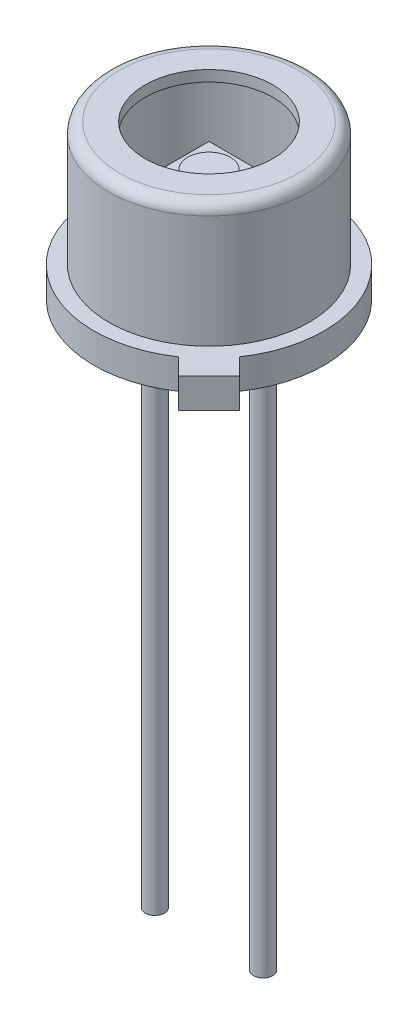
SolidWorks part; units mm, degrees
ref_plane "Front Plane" through (0, 0, 0) normal (0, 0, 1) x (1, 0, 0)
ref_plane "Top Plane" through (0, 0, 0) normal (0, 1, 0) x (1, 0, 0)
ref_plane "Right Plane" through (0, 0, 0) normal (1, 0, 0) x (0, 0, -1)
sketch "Sketch1" plane through (0, 0, 0) normal (0, 0, 1) x (1, 0, 0)
  line L0 (0, 0) -> (0, 37.7864) construction
  line L2 (2.7, 0) -> (2.7, 0.7)
  line L3 (2.7, 0.7) -> (2.35, 0.7)
  line L6 (2.35, 0.7) -> (2.35, 3.346)
  line L7 (2.096, 3.6) -> (1.5, 3.6)
  arc A0 (2.35, 3.346) -> (2.096, 3.6) centre (2.096, 3.346) ccw
  dimension "D7" = 0.254
  dimension "D1" = 0.7
  dimension "D2" = 4.7
  dimension "D4" = 5.4
  dimension "D6" = 3.6
  dimension "D8" = 3
revolve "Revolve-Thin2" add sketch "Sketch1" angle 360 about L0
sketch "Sketch2" plane through (0, 0, 0) normal (0, -1, 0) x (1, 0, 0)
  circle A1 centre (0, 0) radius 2.7
  circle A2 centre (0, 0) radius 2.7
  dimension "D1" = 0
extrude "Boss-Extrude1" add sketch "Sketch2" against normal up to surface (0.446 mm away) up to face at (0, 0.446, -2.096)
sketch "Sketch3" plane through (0, 0, 0) normal (0, -1, 0) x (1, 0, 0)
  line L0 (0.6, 0.6) -> (-0.6, -0.6) construction
  line L1 (-0.6, 0.6) -> (0.6, 0.6)
  line L2 (-0.6, 0.6) -> (-0.6, -0.6)
  line L3 (-0.6, -0.6) -> (0.6, -0.6)
  line L4 (0.6, 0.6) -> (0.6, -0.6)
  dimension "D1" = 1.2
extrude "Boss-Extrude2" add sketch "Sketch3" along normal blind 0.05 from offset 2.6 separate body offset against normal yes
sketch "Sketch8" plane through (0, 2.6, 0) normal (0, 1, 0) x (-1, 0, 0)
  circle A0 centre (0, 0) radius 0.5
  dimension "D1" = 1
extrude "Boss-Extrude6" add sketch "Sketch8" along normal blind 0.03
sketch "Sketch5" plane through (0, 0, 0) normal (0, -1, 0) x (1, 0, 0)
  line L0 (0, 0) -> (-1.27, 0) construction
  line L1 (0, 0) -> (1.27, 0) construction
  circle A0 centre (0, 0) radius 1.27 construction
  circle A1 centre (-1.27, 0) radius 0.225
  circle A2 centre (1.27, 0) radius 0.225
  circle A3 centre (-1.27, 0) radius 0.225
  circle A4 centre (0, 0) radius 2.7 construction
  circle A5 centre (0, -1.27) radius 0.225
  dimension "D1" = 2.54
  dimension "D2" = 0.45
  dimension "D3" = 0.45
sketch "Sketch10" plane through (0, 0, 0) normal (0, -1, 0) x (1, 0, 0)
  line L0 (0, 0) -> (2.7, 0) construction
  line L1 (0, 0) -> (2.3143, 2.3143) construction
  line L8 (1.5203, 2.2313) -> (2.2313, 1.5203)
  line L10 (2.2313, 1.5203) -> (2.6183, 1.9072)
  line L11 (1.9072, 2.6183) -> (2.6183, 1.9072)
  line L12 (1.5203, 2.2313) -> (1.9072, 2.6183)
  circle A0 centre (0, 0) radius 2.7 construction
  dimension "D3" = 0.5472
  dimension "D1" = 45
  dimension "D2" = 1.0055
extrude "Boss-Extrude7" add sketch "Sketch10" against normal blind 0.7
extrude "Boss-Extrude8" add sketch "Sketch5" along normal blind 13 contours A1 | A5 | A2
